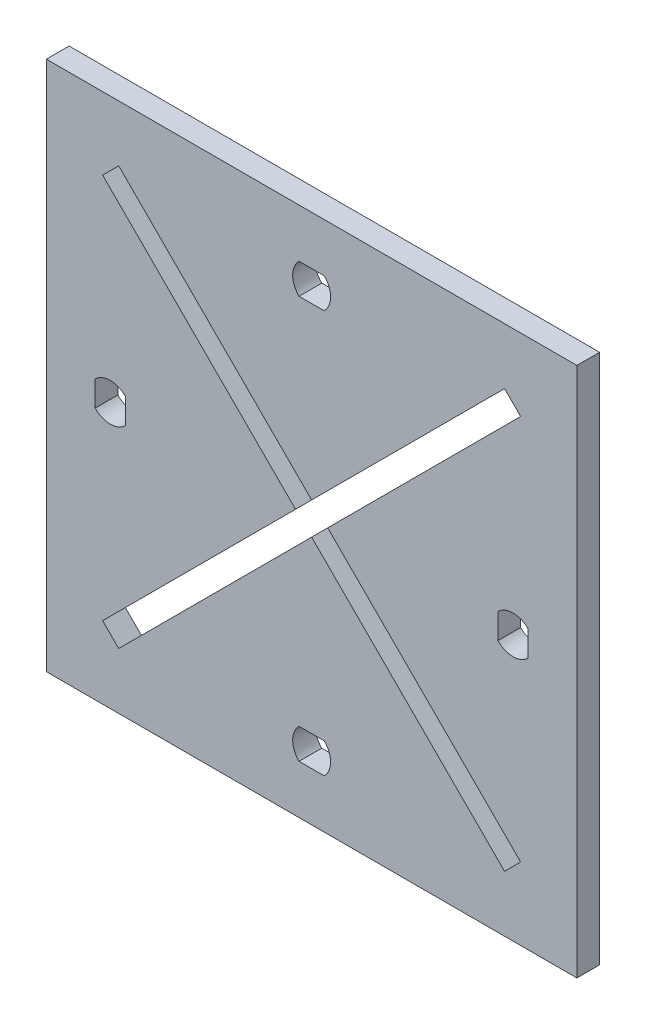
SolidWorks part; units mm, degrees
ref_plane "Plano frontal" through (0, 0, 0) normal (0, 0, 1) x (1, 0, 0)
ref_plane "Plano superior" through (0, 0, 0) normal (0, 1, 0) x (1, 0, 0)
ref_plane "Plano direito" through (0, 0, 0) normal (1, 0, 0) x (0, 0, -1)
sketch "Esboço1" plane through (0, 0, 0) normal (0, 0, 1) x (1, 0, 0)
  line L0 (26.9498, -2.9995) -> (26.9498, -6.3285)
  line L1 (-32.622, 30.336) -> (37.378, 30.336)
  line L2 (-32.622, 30.336) -> (-32.622, -39.664)
  line L3 (-32.622, -39.664) -> (37.378, -39.664)
  line L4 (37.378, 30.336) -> (37.378, -39.664)
  line L7 (2.378, 30.336) -> (2.378, -39.664) construction
  line L8 (-32.622, 30.336) -> (37.378, -39.664) construction
  line L9 (30.9498, -2.9995) -> (30.9498, -6.3285)
  line L10 (37.378, -4.664) -> (-32.622, -4.664) construction
  line L11 (0.7135, -33.2358) -> (4.0425, -33.2358)
  line L12 (0.7135, -29.2358) -> (4.0425, -29.2358)
  line L13 (-22.1937, -2.9995) -> (-22.1937, -6.3285)
  line L14 (-26.1937, -2.9995) -> (-26.1937, -6.3285)
  line L15 (0.7135, 23.9078) -> (4.0425, 23.9078)
  line L16 (0.7135, 19.9078) -> (4.0425, 19.9078)
  line L17 (-25.1991, 20.7919) -> (-23.0778, 22.9132)
  line L18 (-23.0778, 22.9132) -> (29.9552, -30.1198)
  line L19 (29.9552, -30.1198) -> (27.8339, -32.2412)
  line L20 (27.8339, -32.2412) -> (-25.1991, 20.7919)
  line L21 (-25.1991, -30.1198) -> (-23.0778, -32.2412)
  line L22 (27.8339, 22.9132) -> (-25.1991, -30.1198)
  line L23 (29.9552, 20.7919) -> (27.8339, 22.9132)
  line L24 (-23.0778, -32.2412) -> (29.9552, 20.7919)
  arc A2 (26.9498, -6.3285) -> (30.9498, -6.3285) centre (28.9498, -4.3525) ccw
  arc A3 (26.9498, -2.9995) -> (30.9498, -2.9995) centre (28.9498, -4.9755) cw
  arc A4 (4.0425, -29.2358) -> (4.0425, -33.2358) centre (2.0665, -31.2358) cw
  arc A5 (0.7135, -29.2358) -> (0.7135, -33.2358) centre (2.6896, -31.2358) ccw
  arc A6 (-22.1937, -6.3285) -> (-26.1937, -6.3285) centre (-24.1937, -4.3525) cw
  arc A7 (-22.1937, -2.9995) -> (-26.1937, -2.9995) centre (-24.1937, -4.9755) ccw
  arc A8 (0.7135, 19.9078) -> (0.7135, 23.9078) centre (2.6896, 21.9078) cw
  arc A9 (4.0425, 19.9078) -> (4.0425, 23.9078) centre (2.0665, 21.9078) ccw
  dimension "D1" = 70
  dimension "D2" = 70
  dimension "D3" = 4
  dimension "D4" = 3
  dimension "D5" = 1.5
  dimension "D6" = 75
  dimension "D7" = 36
extrude "Ressalto-extrusão2" add sketch "Esboço1" along normal blind 3 contours L4 L1 L2 L3 A9 L16 A8 L15 A7 L13 A6 L14 A5 L12 A4 L11 L24 L21 L22 L20 L17 L18 L23 L19 L0 A3 L9 A2
